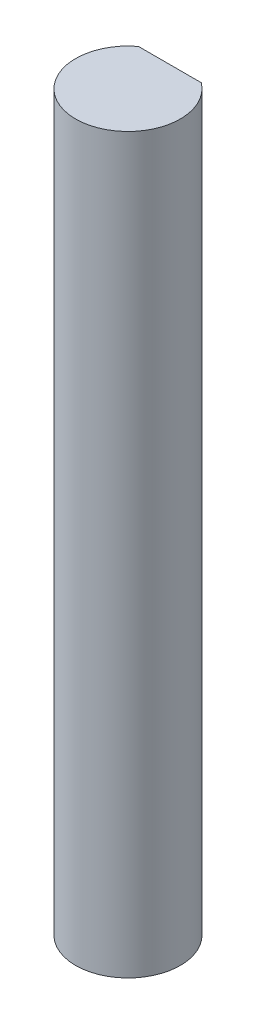
SolidWorks part; units mm, degrees
ref_plane "Front Plane" through (0, 0, 0) normal (0, 0, 1) x (1, 0, 0)
ref_plane "Top Plane" through (0, 0, 0) normal (0, 1, 0) x (1, 0, 0)
ref_plane "Right Plane" through (0, 0, 0) normal (1, 0, 0) x (0, 0, -1)
sketch "Sketch1" plane through (0, 0, 0) normal (0, 1, 0) x (1, 0, 0)
  line L0 (-1.905, 2.54) -> (1.905, 2.54)
  arc A0 (-1.905, 2.54) -> (1.905, 2.54) centre (0, 0) ccw
  dimension "D1" = 6.35
  dimension "D2" = 2.54
extrude "Boss-Extrude1" add sketch "Sketch1" along normal blind 44.45
